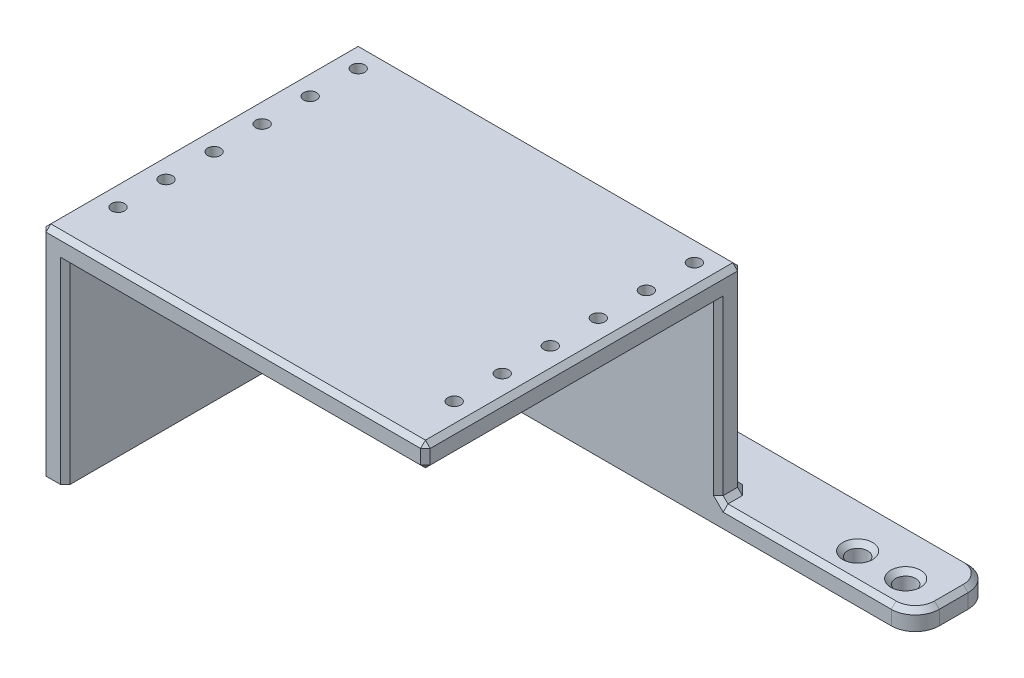
SolidWorks part; units mm, degrees
ref_plane "Front Plane" through (0, 0, 0) normal (0, 0, 1) x (1, 0, 0)
ref_plane "Top Plane" through (0, 0, 0) normal (0, 1, 0) x (1, 0, 0)
ref_plane "Right Plane" through (0, 0, 0) normal (1, 0, 0) x (0, 0, -1)
sketch "Sketch1" plane through (0, 0, 0) normal (0, 1, 0) x (1, 0, 0)
  line L0 (-58.8413, 11.6822) -> (52.1587, 11.6822)
  line L3 (57.1587, 6.6822) -> (57.1587, 0.6822)
  line L4 (52.1587, -4.3178) -> (-63.8413, -4.3178)
  line L5 (-63.8413, -4.3178) -> (-63.8413, 6.6822)
  circle A0 centre (-58.8413, 6.6822) radius 2.1
  circle A1 centre (39.1587, 1.6822) radius 2.1
  circle A2 centre (49.1587, 1.6822) radius 2.1
  arc A5 (-58.8413, 11.6822) -> (-63.8413, 6.6822) centre (-58.8413, 6.6822) ccw
  arc A6 (52.1587, -4.3178) -> (57.1587, 0.6822) centre (52.1587, 0.6822) ccw
  arc A7 (57.1587, 6.6822) -> (52.1587, 11.6822) centre (52.1587, 6.6822) ccw
  dimension "D2" = 4.2
  dimension "D3" = 98
  dimension "D5" = 10
  dimension "D7" = 5
  dimension "D1" = 10
  dimension "D4" = 5
  dimension "D6" = 8
  dimension "D8" = 6
extrude "Boss-Extrude1" add sketch "Sketch1" along normal blind 4
sketch "Sketch2" plane through (0, 4, 0) normal (0, 1, 0) x (1, 0, 0)
  line L1 (-63.8413, -4.3178) -> (16.1587, -4.3178)
  line L2 (-63.8413, -4.3178) -> (-63.8413, 0.6822)
  line L3 (-63.8413, 0.6822) -> (16.1587, 0.6822)
  line L4 (16.1587, -4.3178) -> (16.1587, 0.6822)
  dimension "D1" = 5
  dimension "D2" = 80
extrude "Boss-Extrude2" add sketch "Sketch2" along normal blind 36
sketch "Sketch3" plane through (0, 0, 4.3178) normal (0, 0, 1) x (1, 0, 0)
  line L0 (-63.8413, 0) -> (52.1587, 0) construction
  line L1 (-63.8413, 40) -> (-58.8413, 40)
  line L2 (-63.8413, 40) -> (-63.8413, 0)
  line L3 (-63.8413, 0) -> (-58.8413, 0)
  line L4 (-58.8413, 40) -> (-58.8413, 0)
  dimension "D1" = 5
extrude "Boss-Extrude3" add sketch "Sketch3" along normal blind 61
sketch "Sketch4" plane through (0, 40, 0) normal (0, 1, 0) x (1, 0, 0)
  line L1 (-63.8413, -65.3178) -> (16.1587, -65.3178)
  line L2 (-63.8413, -65.3178) -> (-63.8413, 0.6822)
  line L3 (-63.8413, 0.6822) -> (16.1587, 0.6822)
  line L4 (16.1587, -65.3178) -> (16.1587, 0.6822)
extrude "Boss-Extrude4" add sketch "Sketch4" along normal blind 5
chamfer "Chamfer2" distance 1 angle 45 24 edges at (49.1587, 4, 0.4178) (-58.8413, 4, -4.5822) (39.1587, 4, 0.4178) (-63.8413, 24.5, -0.6822) (-23.8413, 45, -0.6822) (16.1587, 22, 4.3178) (16.1587, 40, 34.8178) (-58.8413, 20, 65.3178) (-21.3413, 40, 65.3178) (16.1587, 42.5, 65.3178) (-63.8413, 4, -3.6822) (-62.3769, 4, -10.2178) (-3.3413, 4, -11.6822) (55.6942, 4, -10.2178) (57.1587, 4, -3.6822) (55.6942, 4, 2.8533) (34.1587, 4, 4.3178) (16.1587, 4, 1.8178) (-23.8413, 4, -0.6822) (16.1587, 24.5, -0.6822) (16.1587, 45, 32.3178) (-23.8413, 45, 65.3178) (-63.8413, 45, 32.3178) (-63.8413, 22.5, 65.3178)
sketch "Sketch5" plane through (0, 45, 0) normal (0, 1, 0) x (1, 0, 0)
  line L0 (16.1587, -0.3178) -> (16.1587, -64.3178) construction
  line L1 (-58.8413, -4.3178) -> (11.1587, -4.3178) construction
  line L2 (-58.8413, -4.3178) -> (-58.8413, -60.3178) construction
  line L3 (-58.8413, -60.3178) -> (11.1587, -60.3178) construction
  line L4 (11.1587, -4.3178) -> (11.1587, -60.3178) construction
  line L5 (15.1587, -65.3178) -> (-62.8413, -65.3178) construction
  line L6 (-63.8413, -64.3178) -> (-63.8413, -0.3178) construction
  line L7 (-62.8413, 0.6822) -> (15.1587, 0.6822) construction
  circle A0 centre (11.1587, -4.3178) radius 1.35
  circle A1 centre (-58.8413, -4.3178) radius 1.35
  circle A2 centre (-58.8413, -14.3178) radius 1.35
  circle A3 centre (11.1587, -14.3178) radius 1.35
  circle A4 centre (-58.8413, -24.3178) radius 1.35
  circle A5 centre (11.1587, -24.3178) radius 1.35
  circle A6 centre (-58.8413, -34.3178) radius 1.35
  circle A7 centre (11.1587, -34.3178) radius 1.35
  circle A8 centre (-58.8413, -44.3178) radius 1.35
  circle A9 centre (11.1587, -44.3178) radius 1.35
  circle A10 centre (-58.8413, -54.3178) radius 1.35
  circle A11 centre (11.1587, -54.3178) radius 1.35
  dimension "D5" = 2.7
  dimension "D1" = 5
  dimension "D2" = 5
  dimension "D3" = 5
  dimension "D4" = 5
  dimension "D6" = 6
extrude "Cut-Extrude1" cut sketch "Sketch5" against normal blind 5
equation "\"D3@Sketch5\"=\"D1@Sketch5\""
equation "\"D4@Sketch5\"=\"D1@Sketch5\""
